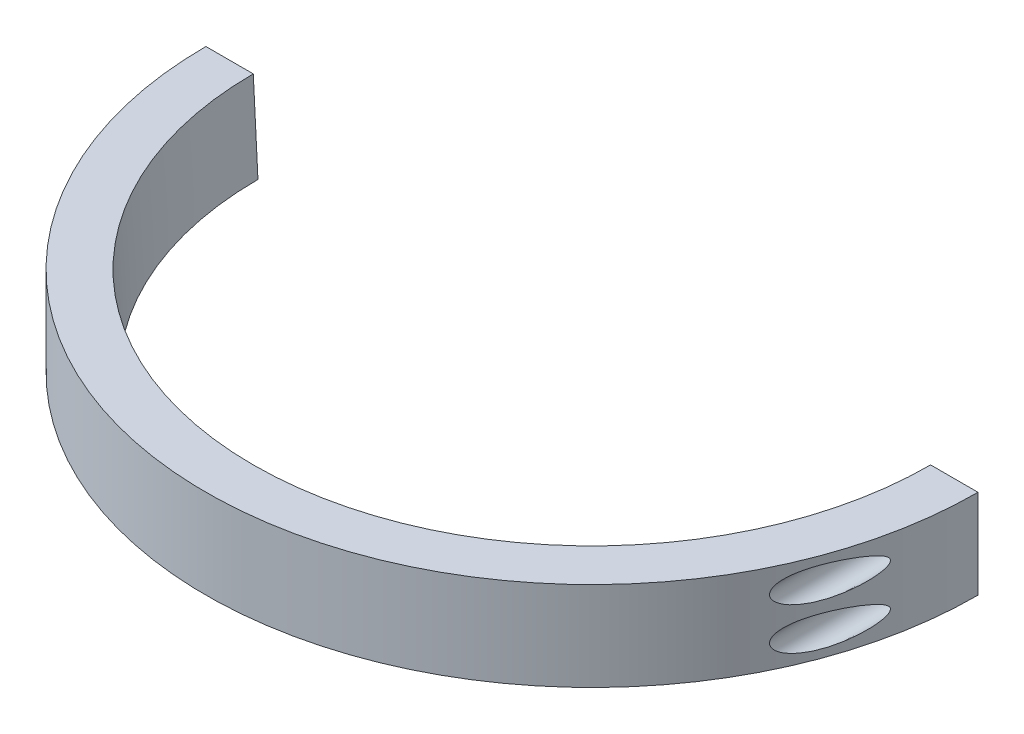
SolidWorks part; units mm, degrees
material "ABS"
ref_plane "Front Plane" through (0, 0, 0) normal (0, 0, 1) x (1, 0, 0)
ref_plane "Top Plane" through (0, 0, 0) normal (0, 1, 0) x (1, 0, 0)
ref_plane "Right Plane" through (0, 0, 0) normal (1, 0, 0) x (0, 0, -1)
sketch "REFERENCE" plane through (0, 0, 0) normal (0, 0, 1) x (1, 0, 0)
  line L0 (0, 0) -> (45, 0) construction
  line L1 (0, 50.3555) -> (0, -50.3555) construction
  line L2 (45, 50.3555) -> (45, -50.3555) construction
  line L3 (45, 0) -> (42.5, -47.7028) construction
  line L4 (40, -105) -> (42.1213, -107.1213) construction
  line L5 (42.5, -47.7028) -> (45.5, -47.7028) construction
  line L6 (45, 0) -> (48, 0) construction
  line L7 (48, 0) -> (45.5, -47.7028) construction
  line L8 (0, -50.3555) -> (0, -113.6539) construction
  arc A0 (42.5, -47.7028) -> (40, -105) centre (0, -74.5516) cw construction
  arc A1 (45.5, -47.7028) -> (42.1213, -107.1213) centre (0, -74.9209) cw construction
  point P5 (0, 0)
  point P8 (45, 0)
  point P9 (45, 0)
  dimension "D7" = 50.2703
  dimension "D1" = 45
  dimension "D2" = 3
  dimension "D3" = 105
  dimension "D4" = 3
  dimension "D5" = 40
  dimension "D6" = 42.5
sketch "Sketch3" plane through (0, 0, 0) normal (0, 0, 1) x (1, 0, 0)
  line L5 (48.25, 0) -> (47.5844, -12.7)
  line L6 (47.5844, -12.7) -> (55, -12.7)
  line L7 (55, -12.7) -> (55, 0)
  line L8 (55, 0) -> (48.25, 0)
  line L9 (48, 0) -> (45.5, -47.7028) construction
  dimension "D1" = 48.25
  dimension "D2" = 55
  dimension "D3" = 12.7
revolve "Revolve2" add sketch "Sketch3" angle 180 about L1
ref_plane "Plane1" through (0, 0, 55) normal (0, 0, 1) x (1, 0, 0)
hole_wizard "CBORE for M2 SHCS1" positions "Sketch6" profile "Sketch8" counterbore size "M2" standard "ANSI Metric" end condition through all
sketch "Sketch6" plane through (0, 0, 55) normal (0, 0, 1) x (1, 0, 0)
  line L0 (51.625, -3.35) -> (51.625, -9.35)
  line L2 (55, 0) -> (48.25, 0) construction
  line L3 (55, -12.7) -> (55, 0) construction
  point P0 (51.625, -3.35)
  point P2 (51.625, -9.35)
  point P12 (51.625, 0)
  point P13 (51.625, -6.35)
  point P16 (55, -6.35)
  dimension "D1" = 0
  dimension "D2" = 0
  dimension "D3" = 6
sketch "Sketch8" plane through (51.625, -3.35, 55) normal (1, 0, 0) x (0, -1, 0)
  line L0 (0, 0) -> (0, 55)
  line L1 (0, 55) -> (1.1, 55)
  line L3 (1.1, 55) -> (1.1, 50)
  line L4 (1.1, 50) -> (2.2, 50)
  line L5 (2.2, 50) -> (2.2, 0)
  line L7 (2.2, 0) -> (0, 0)
  line L11 (0, -6.35) -> (0, 107.95) construction
  dimension "Thru Hole Dia." = 2.2
  dimension "Thru Hole Depth" = 55
  dimension "C'Bore Dia." = 4.4
  dimension "C'Bore Depth" = 50
mirror "Mirror1" about plane through (0, 0, 0) normal (1, 0, 0) of "CBORE for M2 SHCS1"
sketch "Sketch9" [suppressed] plane through (0, 0, 55) normal (0, 0, 1) x (1, 0, 0)
  line L0 (51.625, -3.35) -> (51.625, -9.35) construction
  line L1 (55, 0) -> (48.25, 0) construction
  line L2 (55, -12.7) -> (55, 0) construction
  line L4 (53.725, -4.5624) -> (53.725, -2.1376)
  line L5 (53.725, -2.1376) -> (51.625, -0.9251)
  line L6 (51.625, -0.9251) -> (49.525, -2.1376)
  line L7 (49.525, -2.1376) -> (49.525, -4.5624)
  line L8 (49.525, -4.5624) -> (51.625, -5.7749)
  line L9 (51.625, -5.7749) -> (53.725, -4.5624)
  line L10 (53.725, -10.5624) -> (53.725, -8.1376)
  line L11 (53.725, -8.1376) -> (51.625, -6.9251)
  line L12 (51.625, -6.9251) -> (49.525, -8.1376)
  line L13 (49.525, -8.1376) -> (49.525, -10.5624)
  line L14 (49.525, -10.5624) -> (51.625, -11.7749)
  line L15 (51.625, -11.7749) -> (53.725, -10.5624)
  circle A0 centre (51.625, -3.35) radius 2.1 construction
  circle A1 centre (51.625, -9.35) radius 2.1 construction
  point P0 (51.625, -3.35)
  point P1 (51.625, -9.35)
  point P6 (51.625, 0)
  point P7 (51.625, -6.35)
  point P10 (55, -6.35)
  dimension "D1" = 0
  dimension "D2" = 0
  dimension "D3" = 6
  dimension "D4" = 4.2
  dimension "D5" = 4.2
extrude "Cut-Extrude1" [suppressed] cut sketch "Sketch9" against normal blind 50
hole_wizard "Ø2.0mm Dowel Hole1" [suppressed] positions "Sketch10" profile "Sketch11" hole size "Ø2.0" standard "ANSI Metric"
sketch "Sketch10" plane through (0, 0, 5) normal (0, 0, 1) x (1, 0, 0)
  line L0 (53.725, -2.1376) -> (49.525, -4.5624)
  line L2 (49.525, -2.1376) -> (53.725, -4.5624)
  line L4 (53.725, -8.1376) -> (49.525, -10.5624)
  line L6 (49.525, -8.1376) -> (53.725, -10.5624)
  line L7 (53.725, -8.1376) -> (53.725, -10.5624) construction
  line L8 (53.725, -10.5624) -> (53.725, -8.1376) construction
  point P29 (51.625, -3.35)
  point P31 (51.625, -9.35)
sketch "Sketch11" plane through (51.625, -9.35, 5) normal (1, 0, 0) x (0, -1, 0)
  line L0 (0, 0) -> (0, 5)
  line L1 (0, 5) -> (1.15, 5)
  line L2 (1.15, 5) -> (1.15, 0)
  line L5 (1.15, 0) -> (0, 0)
  line L11 (0, -6.35) -> (0, 107.95) construction
  dimension "Thru Hole Dia." = 2.3
  dimension "Thru Hole Depth" = 5
mirror "Mirror2" [suppressed] about plane through (0, 0, 0) normal (1, 0, 0)
ref_plane "Plane2" through (0, 0, 0) normal (-0.7071, 0, 0.7071) x (0.7071, 0, 0.7071)
sketch "Sketch13" plane through (0, 0, 0) normal (-0.7071, 0, 0.7071) x (0.7071, 0, 0.7071)
  line L0 (55, 0) -> (-38.8909, 0) construction
  circle A0 centre (0, -6.35) radius 1.65
  dimension "D3" = 3.3
  dimension "D1" = 6.35
  dimension "D2" = 0
extrude "Cut-Extrude2" cut sketch "Sketch13" against normal mid plane 200
